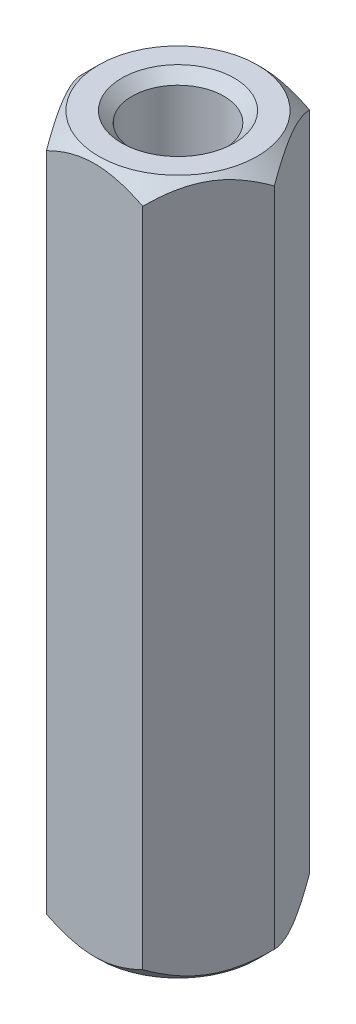
SolidWorks part; units mm, degrees
ref_plane "Front" through (0, 0, 0) normal (0, 0, 1) x (1, 0, 0)
ref_plane "Top" through (0, 0, 0) normal (0, 1, 0) x (1, 0, 0)
ref_plane "Right" through (0, 0, 0) normal (1, 0, 0) x (0, 0, -1)
sketch "Sketch1" plane through (0, 0, 0) normal (0, 1, 0) x (1, 0, 0)
  line L1 (1.7321, 3) -> (-1.7321, 3)
  line L2 (-1.7321, 3) -> (-3.4641, 0)
  line L3 (-3.4641, 0) -> (-1.7321, -3)
  line L4 (-1.7321, -3) -> (1.7321, -3)
  line L5 (1.7321, -3) -> (3.4641, 0)
  line L6 (3.4641, 0) -> (1.7321, 3)
  circle A0 centre (0, 0) radius 3 construction
  dimension "D1" = 6
extrude "Boss-Extrude1" add sketch "Sketch1" along normal blind 25
hole_wizard "M4 Tapped Hole1" positions "Sketch3" profile "Sketch2" tap size "M4" standard "ISO" end condition through all
sketch "Sketch3" plane through (0, 25, 0) normal (0, 1, 0) x (1, 0, 0)
  point P0 (0, 0)
sketch "Sketch2" plane through (0, 25, 0) normal (1, 0, 0) x (0, 0, 1)
  line L0 (0, 0) -> (0, 25)
  line L1 (0, 25) -> (2.025, 25)
  line L2 (1.65, 24.625) -> (1.65, 0.375)
  line L3 (1.65, 0.375) -> (2.025, 0)
  line L5 (2.025, 0) -> (0, 0)
  line L6 (-1.65, 0.375) -> (-2.025, 0) construction
  line L7 (2.025, 25) -> (1.65, 24.625)
  line L8 (-2.025, 25) -> (-1.65, 24.625) construction
  line L11 (0, -6.35) -> (0, 107.95) construction
  dimension "Thru Tap Drill Dia." = 3.3
  dimension "Thru Tap Drill Depth" = 25
  dimension "Near C'Sink Dia." = 4.05
  dimension "Near C'Sink Angle" = 90
  dimension "Far C'Sink Dia." = 4.05
  dimension "Far C'Sink Angle" = 90
cosmetic thread "Hole Thread1" parameters "D2"=4
sketch "Sketch4" plane through (0, 0, 0) normal (0, 0, 1) x (1, 0, 0)
  line L0 (0, 25) -> (0, 0) construction
  line L1 (-1.7321, 25) -> (1.7321, 25) construction
  line L2 (2.85, 0) -> (3.4641, 0.6141)
  line L3 (1.7321, 0) -> (3.4641, 0) construction
  line L4 (3.4641, 25) -> (3.4641, 0) construction
  line L5 (3.4641, 0.6141) -> (3.4641, 0)
  line L6 (3.4641, 0) -> (2.85, 0)
  line L7 (0, 12.5) -> (3.4641, 12.5) construction
  line L8 (3.4641, 25) -> (2.85, 25)
  line L9 (3.4641, 24.3859) -> (3.4641, 25)
  line L10 (2.85, 25) -> (3.4641, 24.3859)
  dimension "D1" = 5.7
  dimension "D2" = 45
revolve "Cut-Revolve1" cut sketch "Sketch4" angle 360 about L0
